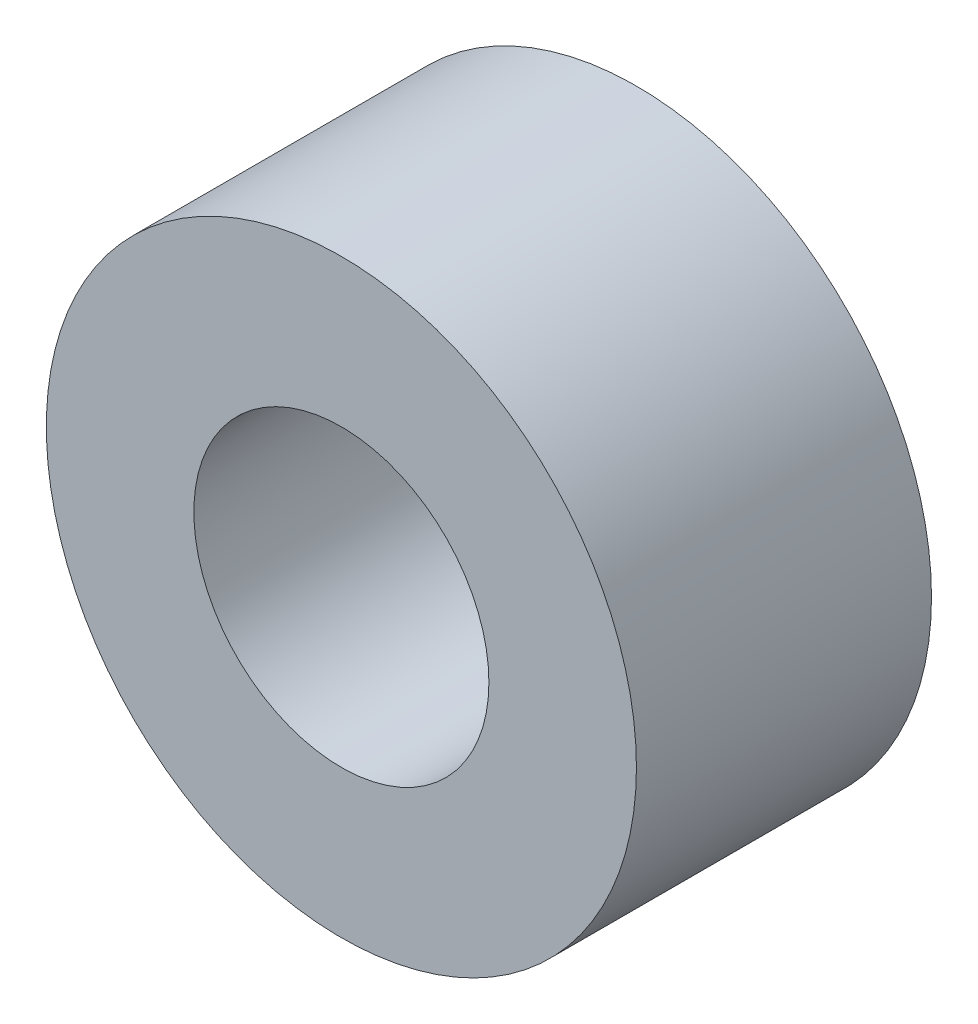
SolidWorks part; units mm, degrees
material "Nylon 101"
ref_plane "Front Plane" through (0, 0, 0) normal (0, 0, 1) x (1, 0, 0)
ref_plane "Top Plane" through (0, 0, 0) normal (0, 1, 0) x (1, 0, 0)
ref_plane "Right Plane" through (0, 0, 0) normal (1, 0, 0) x (0, 0, -1)
sketch "Sketch1" plane through (0, 0, 0) normal (0, 0, 1) x (1, 0, 0)
  circle A0 centre (0, 0) radius 12.7
  dimension "D1" = 25.4
extrude "Boss-Extrude1" add sketch "Sketch1" along normal blind 12.7
sketch "Sketch2" plane through (0, 0, 12.7) normal (0, 0, 1) x (1, 0, 0)
  circle A0 centre (0, 0) radius 6.35
  dimension "D1" = 12.7
extrude "Cut-Extrude1" cut sketch "Sketch2" against normal blind 12.7
